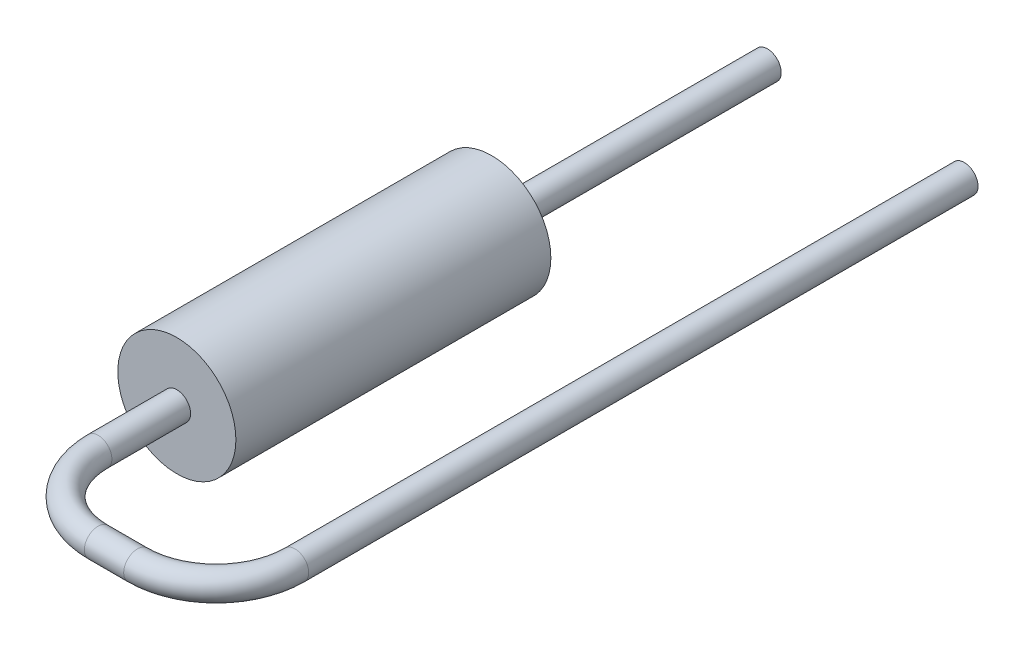
SolidWorks part; units mm, degrees
ref_plane "Front Plane" through (0, 0, 0) normal (0, 0, 1) x (1, 0, 0)
ref_plane "Top Plane" through (0, 0, 0) normal (0, 1, 0) x (1, 0, 0)
ref_plane "Right Plane" through (0, 0, 0) normal (1, 0, 0) x (0, 0, -1)
sketch "Sketch2" plane through (0, 0, 0) normal (0, 0, 1) x (1, 0, 0)
  circle A0 centre (0, 0) radius 1.5
  dimension "D1" = 3
extrude "Resistor Body" add sketch "Sketch2" along normal blind 8
sketch "Lead1 Path" plane through (0, 0, 0) normal (0, 1, 0) x (1, 0, 0)
  line L1 (-1.5, -8) -> (1.5, -8) construction
  line L2 (0, -8) -> (0, 0) construction
  line L3 (0, -8) -> (0, -10)
  line L4 (5, -10) -> (5, 7)
  line L5 (2, -12) -> (3, -12)
  arc A0 (0, -10) -> (2, -12) centre (2, -10) ccw
  arc A1 (5, -10) -> (3, -12) centre (3, -10) cw
  point P11 (0, -12)
  point P14 (5, -12)
  dimension "D4" = 2
  dimension "D1" = 19
  dimension "D2" = 4
  dimension "D3" = 5
sketch "Lead1 Profile" plane through (0, 0, 8) normal (0, 0, 1) x (-1, 0, 0)
  circle A0 centre (0, 0) radius 0.35
  dimension "D1" = 0.7
sweep "Lead1" add profiles "Lead1 Profile" path "Lead1 Path"
sketch "Sketch6" plane through (0, 0, 0) normal (0, 0, -1) x (1, 0, 0)
  circle A0 centre (0, 0) radius 0.35 construction
  circle A1 centre (0, 0) radius 0.35
extrude "Lead2" add sketch "Sketch6" along normal up to surface (7 mm away) up to face at (4.65, 0, -7)
ref_plane "Mounting Plane" through (0, 0, -4) normal (0, 0, 1) x (1, 0, 0)
sketch "Component_Outline" plane through (0, 0, -4) normal (0, 0, 1) x (1, 0, 0)
  line L0 (1.4586, 0.35) -> (5, 0.35)
  line L1 (2, 0.35) -> (0, 0.35) construction
  line L2 (5, -0.35) -> (1.4586, -0.35)
  line L3 (0, -0.35) -> (2, -0.35) construction
  arc A0 (1.4586, 0.35) -> (1.4586, -0.35) centre (0, 0) ccw
  arc A1 (5, 0.35) -> (5, -0.35) centre (5, 0) cw
  dimension "D1" = 1.5
